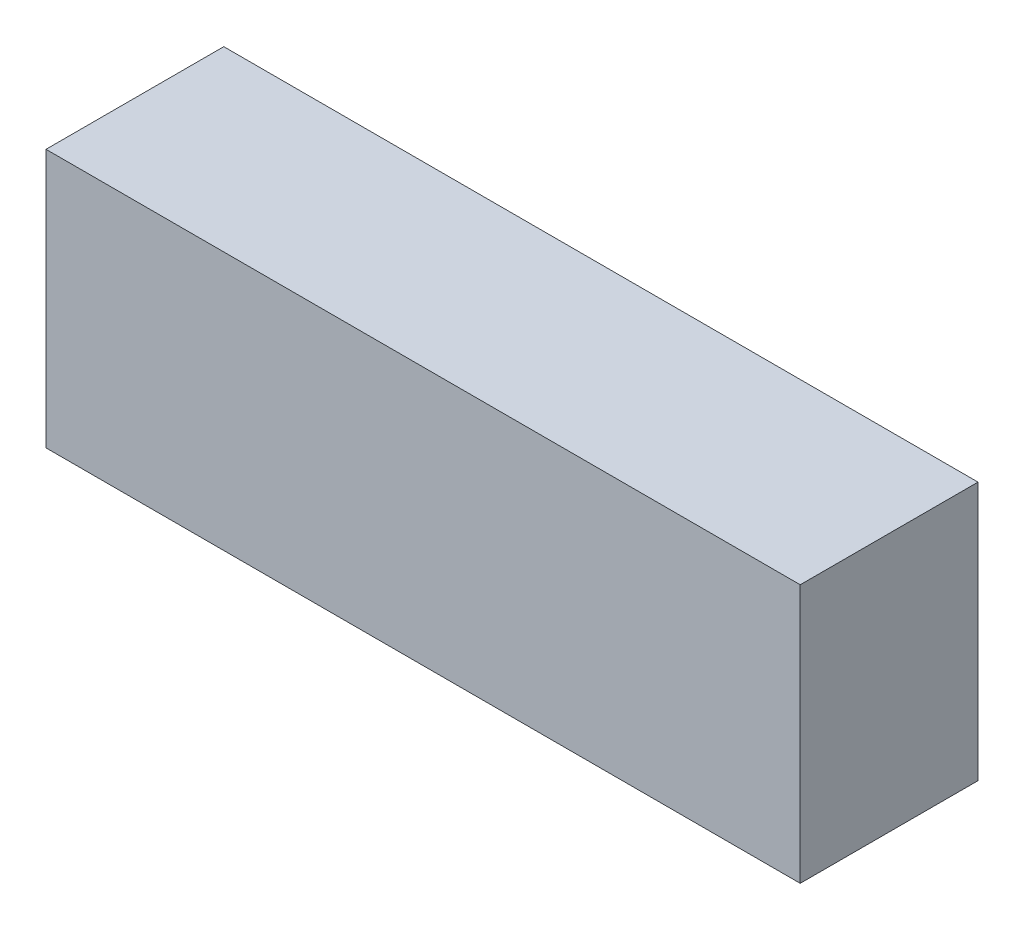
SolidWorks part; units mm, degrees
ref_plane "Front Plane" through (0, 0, 0) normal (0, 0, 1) x (1, 0, 0)
ref_plane "Top Plane" through (0, 0, 0) normal (0, 1, 0) x (1, 0, 0)
ref_plane "Right Plane" through (0, 0, 0) normal (1, 0, 0) x (0, 0, -1)
sketch "Sketch1" plane through (0, 0, 0) normal (0, 0, 1) x (1, 0, 0)
  line L1 (-44.45, 15.24) -> (44.45, 15.24)
  line L2 (-44.45, 15.24) -> (-44.45, -15.24)
  line L3 (-44.45, -15.24) -> (44.45, -15.24)
  line L4 (44.45, 15.24) -> (44.45, -15.24)
  line L5 (-44.45, 15.24) -> (44.45, -15.24) construction
  line L6 (-44.45, -15.24) -> (44.45, 15.24) construction
  point P0 (0, 0)
  dimension "D1" = 30.48
  dimension "D2" = 88.9
extrude "Boss-Extrude1" add sketch "Sketch1" along normal blind 20.955
